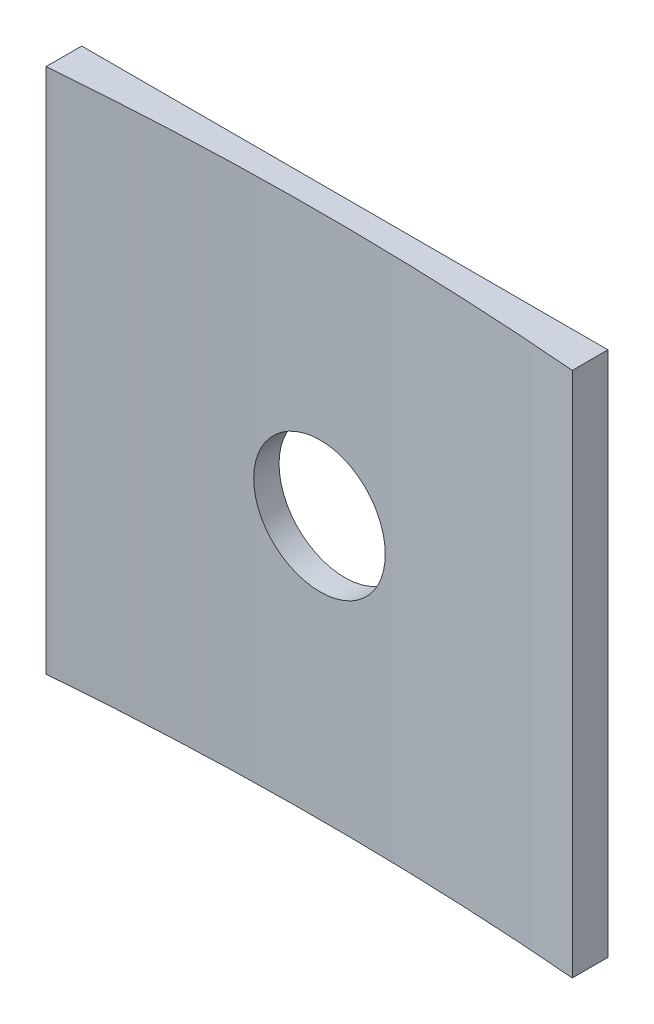
SolidWorks part; units mm, degrees
ref_plane "Front Plane" through (0, 0, 0) normal (0, 0, 1) x (1, 0, 0)
ref_plane "Top Plane" through (0, 0, 0) normal (0, 1, 0) x (1, 0, 0)
ref_plane "Right Plane" through (0, 0, 0) normal (1, 0, 0) x (0, 0, -1)
sketch "Sketch1" plane through (0, 0, 0) normal (0, 1, 0) x (1, 0, 0)
  line L0 (0, 0) -> (0, 152.4) construction
  line L1 (0, 152.4) -> (-12.7, 152.4) construction
  line L2 (0, 152.4) -> (12.7, 152.4) construction
  line L3 (-12.7, 152.4) -> (-12.7, 127) construction
  line L4 (12.7, 152.4) -> (12.7, 127) construction
  line L5 (-12.7, 151.8699) -> (-12.7, 153.5908)
  line L6 (-12.7, 153.5908) -> (12.7, 153.5908)
  line L7 (12.7, 153.5908) -> (12.7, 151.8699)
  arc A0 (0, 152.4) -> (-12.7, 151.8699) centre (0, 0) ccw
  arc A1 (0, 152.4) -> (12.7, 151.8699) centre (0, 0) cw
  dimension "D1" = 152.4
  dimension "D2" = 12.7
  dimension "D3" = 12.7
  dimension "D4" = 25.4
  dimension "D5" = 25.4
  dimension "D6" = 1.7209
extrude "Boss-Extrude1" add sketch "Sketch1" against normal blind 25.4
sketch "Sketch2" plane through (0, 0, -153.5908) normal (0, 0, -1) x (-1, 0, 0)
  line L0 (-12.7, 0) -> (0, 0) construction
  line L1 (0, 0) -> (0, -12.7) construction
  circle A0 centre (0, -12.7) radius 3.175
  dimension "D2" = 6.35
extrude "Cut-Extrude1" cut sketch "Sketch2" against normal blind 1.7209
equation "\"Width\"= 1"
equation "\"D2@Sketch1\"=\"Width\"/2"
equation "\"D3@Sketch1\"=\"Width\"/2"
equation "\"thick\"=0.067753"
equation "\"D6@Sketch1\"=\"thick\""
equation "\"length\"=1"
equation "\"D1@Boss-Extrude1\"=\"length\""
equation "\"D1@Sketch2\"=\"length\"/2"
equation "\"bolt_diameter\" = 0.25"
equation "\"D2@Sketch2\"=\"bolt_diameter\""
equation "\"Outer_Radius\" = 6"
equation "\"D1@Sketch1\"=\"Outer_Radius\""
equation "\"D1@Cut-Extrude1\"=\"thick\""
